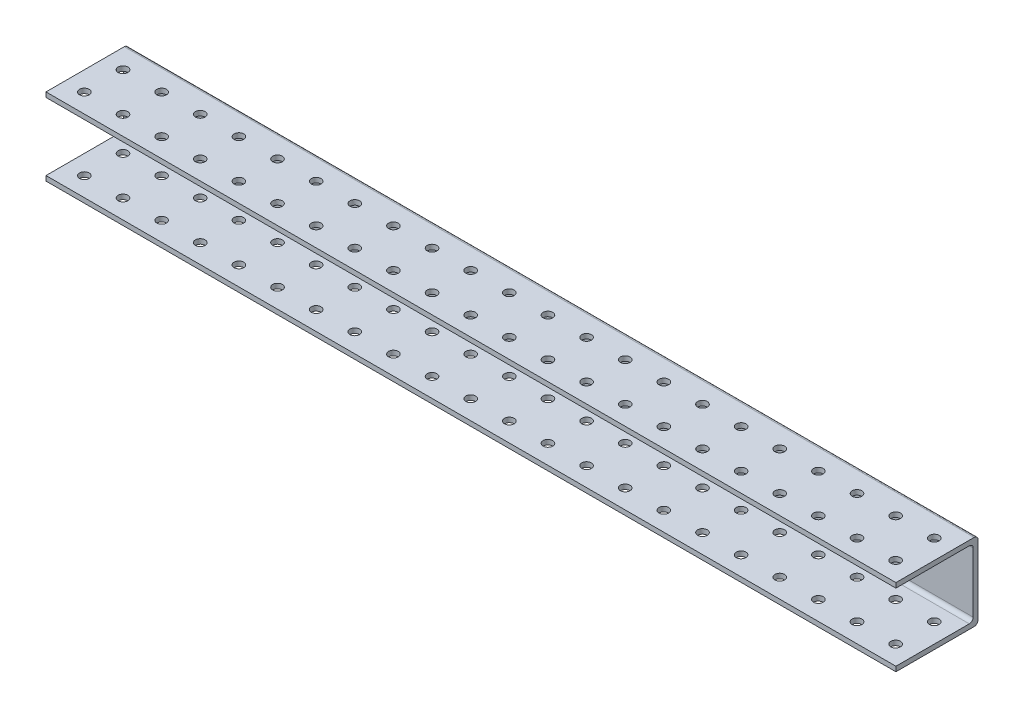
SolidWorks part; units mm, degrees
ref_plane "Front Plane" through (0, 0, 0) normal (0, 0, 1) x (1, 0, 0)
ref_plane "Top Plane" through (0, 0, 0) normal (0, 1, 0) x (1, 0, 0)
ref_plane "Right Plane" through (0, 0, 0) normal (1, 0, 0) x (0, 0, -1)
sketch "Sketch1" plane through (0, 0, 0) normal (0, 0, 1) x (1, 0, 0)
  line L1 (0, 0) -> (558.8, 0)
  line L2 (0, 0) -> (0, 38.1)
  line L3 (0, 38.1) -> (558.8, 38.1)
  line L4 (558.8, 0) -> (558.8, 38.1)
  dimension "D1" = 38.1
  dimension "D2" = 558.8
extrude "Boss-Extrude1" add sketch "Sketch1" along normal blind 3.175
sketch "Sketch2" plane through (0, 0, 3.175) normal (0, 0, 1) x (1, 0, 0)
  line L0 (558.8, 0) -> (558.8, 38.1) construction
  line L1 (0, 38.1) -> (558.8, 38.1)
  line L2 (0, 38.1) -> (0, 34.925)
  line L3 (0, 34.925) -> (558.8, 34.925)
  line L4 (558.8, 38.1) -> (558.8, 34.925)
  line L5 (0, 38.1) -> (0, 0) construction
  line L6 (558.8, 0) -> (0, 0)
  line L7 (558.8, 0) -> (558.8, 3.175)
  line L8 (558.8, 3.175) -> (0, 3.175)
  line L9 (0, 0) -> (0, 3.175)
  dimension "D1" = 3.175
  dimension "D2" = 3.175
extrude "Boss-Extrude2" add sketch "Sketch2" along normal blind 44.45
fillet "Fillet1" radius 2.54 4 edges at (279.4, 3.175, 3.175) (279.4, 0, 0) (279.4, 38.1, 0)
sketch "Sketch3" plane through (0, 38.1, 0) normal (0, 1, 0) x (1, 0, 0)
  line L0 (0, -47.625) -> (0, -2.54) construction
  line L1 (558.8, -47.625) -> (0, -47.625) construction
  circle A0 centre (12.7, -35.1028) radius 3.175
  circle A1 centre (38.1, -35.1028) radius 3.175
  circle A2 centre (63.5, -35.1028) radius 3.175
  circle A3 centre (88.9, -35.1028) radius 3.175
  circle A4 centre (114.3, -35.1028) radius 3.175
  circle A5 centre (139.7, -35.1028) radius 3.175
  circle A6 centre (165.1, -35.1028) radius 3.175
  circle A7 centre (190.5, -35.1028) radius 3.175
  circle A8 centre (215.9, -35.1028) radius 3.175
  circle A9 centre (241.3, -35.1028) radius 3.175
  circle A10 centre (266.7, -35.1028) radius 3.175
  circle A11 centre (292.1, -35.1028) radius 3.175
  circle A12 centre (317.5, -35.1028) radius 3.175
  circle A13 centre (342.9, -35.1028) radius 3.175
  circle A14 centre (368.3, -35.1028) radius 3.175
  circle A15 centre (393.7, -35.1028) radius 3.175
  circle A16 centre (419.1, -35.1028) radius 3.175
  circle A17 centre (444.5, -35.1028) radius 3.175
  circle A18 centre (469.9, -35.1028) radius 3.175
  circle A19 centre (495.3, -35.1028) radius 3.175
  circle A20 centre (520.7, -35.1028) radius 3.175
  circle A21 centre (546.1, -35.1028) radius 3.175
  circle A22 centre (38.1, -9.7028) radius 3.175
  circle A23 centre (63.5, -9.7028) radius 3.175
  circle A24 centre (88.9, -9.7028) radius 3.175
  circle A25 centre (114.3, -9.7028) radius 3.175
  circle A26 centre (139.7, -9.7028) radius 3.175
  circle A27 centre (165.1, -9.7028) radius 3.175
  circle A28 centre (190.5, -9.7028) radius 3.175
  circle A29 centre (215.9, -9.7028) radius 3.175
  circle A30 centre (241.3, -9.7028) radius 3.175
  circle A31 centre (266.7, -9.7028) radius 3.175
  circle A32 centre (292.1, -9.7028) radius 3.175
  circle A33 centre (317.5, -9.7028) radius 3.175
  circle A34 centre (342.9, -9.7028) radius 3.175
  circle A35 centre (368.3, -9.7028) radius 3.175
  circle A36 centre (393.7, -9.7028) radius 3.175
  circle A37 centre (419.1, -9.7028) radius 3.175
  circle A38 centre (444.5, -9.7028) radius 3.175
  circle A39 centre (469.9, -9.7028) radius 3.175
  circle A40 centre (495.3, -9.7028) radius 3.175
  circle A41 centre (520.7, -9.7028) radius 3.175
  circle A42 centre (546.1, -9.7028) radius 3.175
  circle A43 centre (12.7, -9.7028) radius 3.175
  dimension "D2" = 6.35
  dimension "D3" = 12.5222
  dimension "D1" = 12.7
  dimension "D4" = 22
  dimension "D5" = 2
extrude "Cut-Extrude1" cut sketch "Sketch3" against normal blind 44.45
sketch "Sketch4" plane through (558.8, 0, 0) normal (1, 0, 0) x (0, 0, -1)
  line L0 (-2.54, 0) -> (-2.54, 25.4)
  line L2 (-2.54, 25.4) -> (13.8855, 25.4)
  line L3 (13.8855, 25.4) -> (13.8855, 51.0825)
  line L4 (13.8855, 51.0825) -> (-54.3325, 51.0825)
  line L5 (-54.3325, 51.0825) -> (-54.3325, 25.4)
  line L6 (-54.3325, 25.4) -> (-2.54, 25.4)
  dimension "D1" = 25.4
extrude "Cut-Extrude2" cut sketch "Sketch4" against normal blind 650.113 contours L2 L3 L4 L5 L6
mirror "Mirror1" about plane through (-91.313, 25.4, 2.54) normal (0, -1, 0) of bodies 104
sketch "Sketch5" plane through (558.8, 0, 0) normal (1, 0, 0) x (0, 0, -1)
  line L0 (-47.625, 47.625) -> (-5.715, 47.625) construction
  line L1 (-47.625, 50.8) -> (6.35, 50.8)
  line L2 (-47.625, 50.8) -> (-47.625, 0)
  line L3 (-47.625, 0) -> (6.35, 0)
  line L4 (6.35, 50.8) -> (6.35, 0)
  line L5 (6.35, 50.8) -> (3.175, 50.8)
  line L6 (6.35, 50.8) -> (6.35, 0)
  line L7 (6.35, 0) -> (3.175, 0)
  line L8 (3.175, 50.8) -> (3.175, 0)
  line L9 (3.175, 50.8) -> (-18.518, 50.8)
  line L10 (3.175, 50.8) -> (3.175, 47.625)
  line L11 (3.175, 47.625) -> (-18.518, 47.625)
  line L12 (-18.518, 50.8) -> (-18.518, 47.625)
  line L13 (-47.625, 3.175) -> (-5.715, 3.175) construction
  line L14 (3.175, 0) -> (-12.7303, 0)
  line L15 (3.175, 0) -> (3.175, 3.175)
  line L16 (3.175, 3.175) -> (-12.7303, 3.175)
  line L17 (-12.7303, 0) -> (-12.7303, 3.175)
  line L18 (-3.9664, 50.8) -> (-3.9664, 47.625)
  line L19 (-5.715, 3.175) -> (-5.715, 0)
  line M4 (0, 2.54) -> (0, 48.26)
  arc M5 (0, 48.26) -> (-2.54, 50.8) centre (-2.54, 48.26) ccw
  line M6 (-2.54, 50.8) -> (-47.625, 50.8)
  arc M15 (-2.54, 0) -> (0, 2.54) centre (-2.54, 2.54) ccw
  dimension "D1" = 53.975
  dimension "D2" = 3.175
extrude "Boss-Extrude3" add sketch "Sketch5" against normal blind 558.8 contours L11 L8 L1 M5 M4 | L18 L11 M6 M4 M5 | L1 L8 L3 L4 | L8 L16 L3 M4 M15 | L16 L19 L14 M15 M4
sketch "Sketch6" plane through (558.8, 0, 0) normal (1, 0, 0) x (0, 0, -1)
  line L0 (-47.625, 3.175) -> (-5.715, 3.175) construction
  line L1 (3.175, 47.625) -> (-29.723, 47.625)
  line L2 (3.175, 47.625) -> (3.175, 3.175)
  line L3 (3.175, 3.175) -> (-29.723, 3.175)
  line L4 (-29.723, 47.625) -> (-29.723, 3.175)
extrude "Cut-Extrude3" cut sketch "Sketch6" against normal blind 558.8
fillet "Fillet2" radius 2.54 4 edges at (279.4, 3.175, -3.175) (279.4, 47.625, -3.175) (279.4, 0, -6.35) (279.4, 50.8, -6.35)
